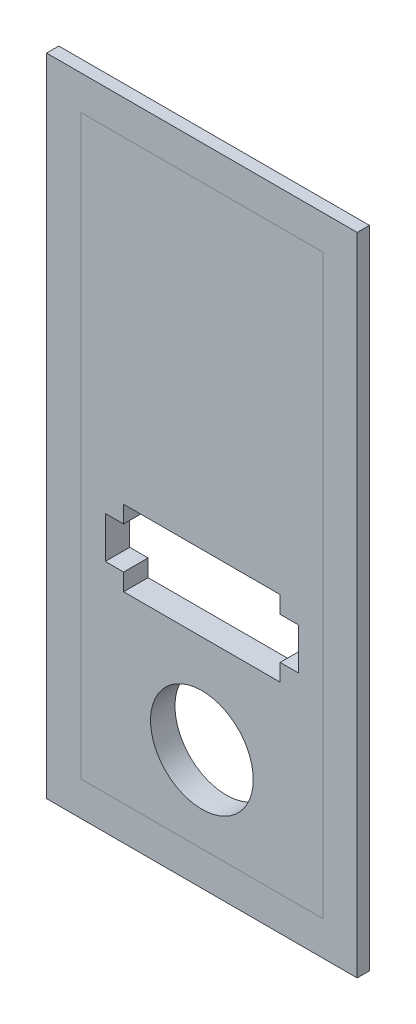
SolidWorks part; units mm, degrees
ref_plane "Plan de face" through (0, 0, 0) normal (0, 0, 1) x (1, 0, 0)
ref_plane "Plan de dessus" through (0, 0, 0) normal (0, 1, 0) x (1, 0, 0)
ref_plane "Plan de droite" through (0, 0, 0) normal (1, 0, 0) x (0, 0, -1)
sketch "Esquisse2" plane through (0, 0, 0) normal (0, 0, 1) x (1, 0, 0)
  line L0 (0, 14.2) -> (0, 8) construction
  line L1 (-6.4, 14.2) -> (6.4, 14.2)
  line L2 (-6.4, 14.2) -> (-6.4, 8)
  line L3 (-6.4, 8) -> (6.4, 8)
  line L4 (6.4, 14.2) -> (6.4, 8)
  line L5 (-7.9, 12.8) -> (-6.4, 12.8)
  line L6 (-7.9, 12.8) -> (-7.9, 9.4)
  line L7 (-7.9, 9.4) -> (-6.4, 9.4)
  line L8 (-6.4, 12.8) -> (-6.4, 9.4)
  line L9 (6.4, 12.8) -> (6.4, 9.4)
  line L10 (7.9, 9.4) -> (6.4, 9.4)
  line L11 (7.9, 12.8) -> (7.9, 9.4)
  line L12 (7.9, 12.8) -> (6.4, 12.8)
  line L14 (-9.9, 40.2) -> (9.9, 40.2)
  line L15 (-9.9, 40.2) -> (-9.9, -7)
  line L16 (-9.9, -7) -> (9.9, -7)
  line L17 (9.9, 40.2) -> (9.9, -7)
  circle A0 centre (0, 0) radius 4.2
  point P7 (0, 8)
  point P8 (-6.4, 11.1)
  point P13 (-6.4, 11.1)
  point P24 (0, -4.2)
  point P25 (0, -7)
  dimension "D1" = 8.4
  dimension "D2" = 8
  dimension "D3" = 6.2
  dimension "D4" = 12.8
  dimension "D5" = 1.5
  dimension "D6" = 3.4
  dimension "D7" = 47.2
  dimension "D8" = 19.8
  dimension "D9" = 7
extrude "Boss.-Extru.1" add sketch "Esquisse2" along normal blind 2 contours L17 L14 L15 L16 A0 L12 L11 L10 L4 L3 L2 L7 L6 L5 L1
sketch "Esquisse3" plane through (0, 0, 2) normal (0, 0, 1) x (1, 0, 0)
  line L0 (-12.7, 43) -> (-12.7, -9.8)
  line L1 (-9.9, 40.2) -> (9.9, 40.2)
  line L2 (-9.9, 40.2) -> (-9.9, -7)
  line L3 (-9.9, -7) -> (9.9, -7)
  line L4 (9.9, 40.2) -> (9.9, -7)
  line L5 (-12.7, -9.8) -> (12.7, -9.8)
  line L6 (12.7, 43) -> (12.7, -9.8)
  line L7 (-12.7, 43) -> (12.7, 43)
  dimension "D1" = 2.8
extrude "Boss.-Extru.2" add sketch "Esquisse3" against normal blind 1 separate body
